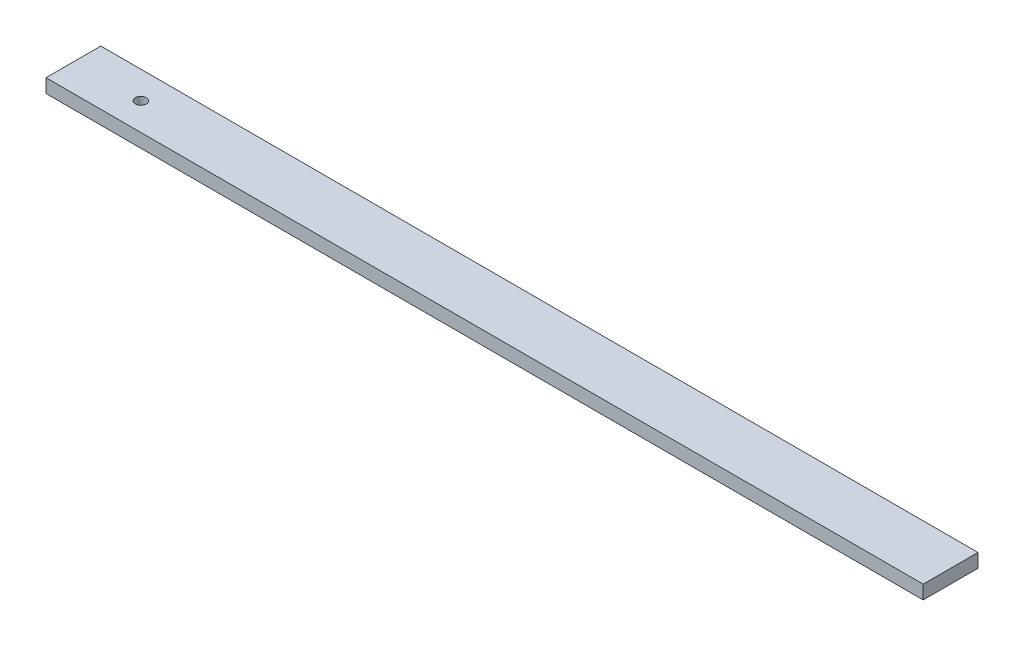
SolidWorks part; units mm, degrees
material "Chrome Stainless Steel"
ref_plane "Front Plane" through (0, 0, 0) normal (0, 0, 1) x (1, 0, 0)
ref_plane "Top Plane" through (0, 0, 0) normal (0, 1, 0) x (1, 0, 0)
ref_plane "Right Plane" through (0, 0, 0) normal (1, 0, 0) x (0, 0, -1)
sketch "Sketch1" plane through (0, 0, 0) normal (1, 0, 0) x (0, 0, -1)
  line L1 (0, 0) -> (1, 0)
  line L2 (0, 0) -> (0, 0.25)
  line L3 (0, 0.25) -> (1, 0.25)
  line L4 (1, 0) -> (1, 0.25)
  dimension "D1" = 0.25
  dimension "D2" = 1
extrude "Boss-Extrude1" add sketch "Sketch1" along normal blind 16
scale "Scale1" scale about centroid uniform scaling yes scale factor 25.4
sketch "Sketch2" plane through (0, 3.3, 0) normal (0, 1, 0) x (1, 0, 0)
  line L0 (-195.2, 0.5) -> (211.2, 0.5) construction
  line L1 (-195.2, 13.2) -> (-195.2, -12.2) construction
  line L2 (211.2, 13.2) -> (211.2, -12.2) construction
  circle A0 centre (-163.958, 0.5) radius 2.54
  dimension "D2" = 5.08
  dimension "D1" = 31.242
extrude "Cut-Extrude1" cut sketch "Sketch2" against normal through all contours A0
